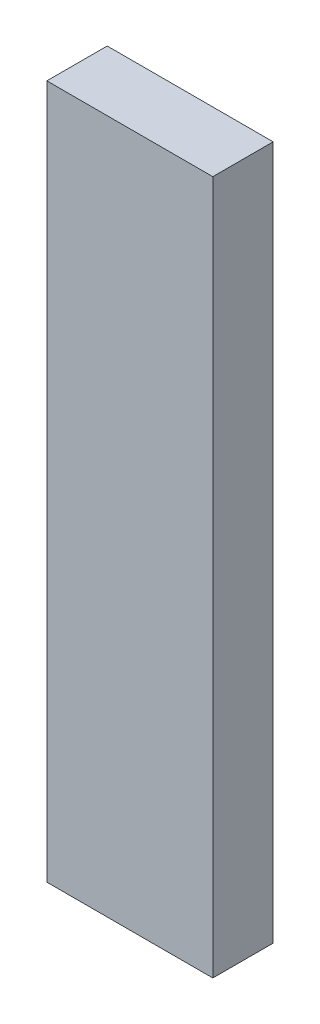
SolidWorks part; units mm, degrees
ref_plane "Спереди" through (0, 0, 0) normal (0, 0, 1) x (1, 0, 0)
ref_plane "Сверху" through (0, 0, 0) normal (0, 1, 0) x (1, 0, 0)
ref_plane "Справа" through (0, 0, 0) normal (1, 0, 0) x (0, 0, -1)
sketch "Эскиз1" plane through (0, 0, 0) normal (0, 1, 0) x (1, 0, 0)
  line L1 (-27.5, 10) -> (27.5, 10)
  line L2 (-27.5, 10) -> (-27.5, -10)
  line L3 (-27.5, -10) -> (27.5, -10)
  line L4 (27.5, 10) -> (27.5, -10)
  line L5 (-27.5, 10) -> (27.5, -10) construction
  line L6 (-27.5, -10) -> (27.5, 10) construction
  point P0 (0, 0)
extrude "Бобышка-Вытянуть1" add sketch "Эскиз1" along normal blind 230
